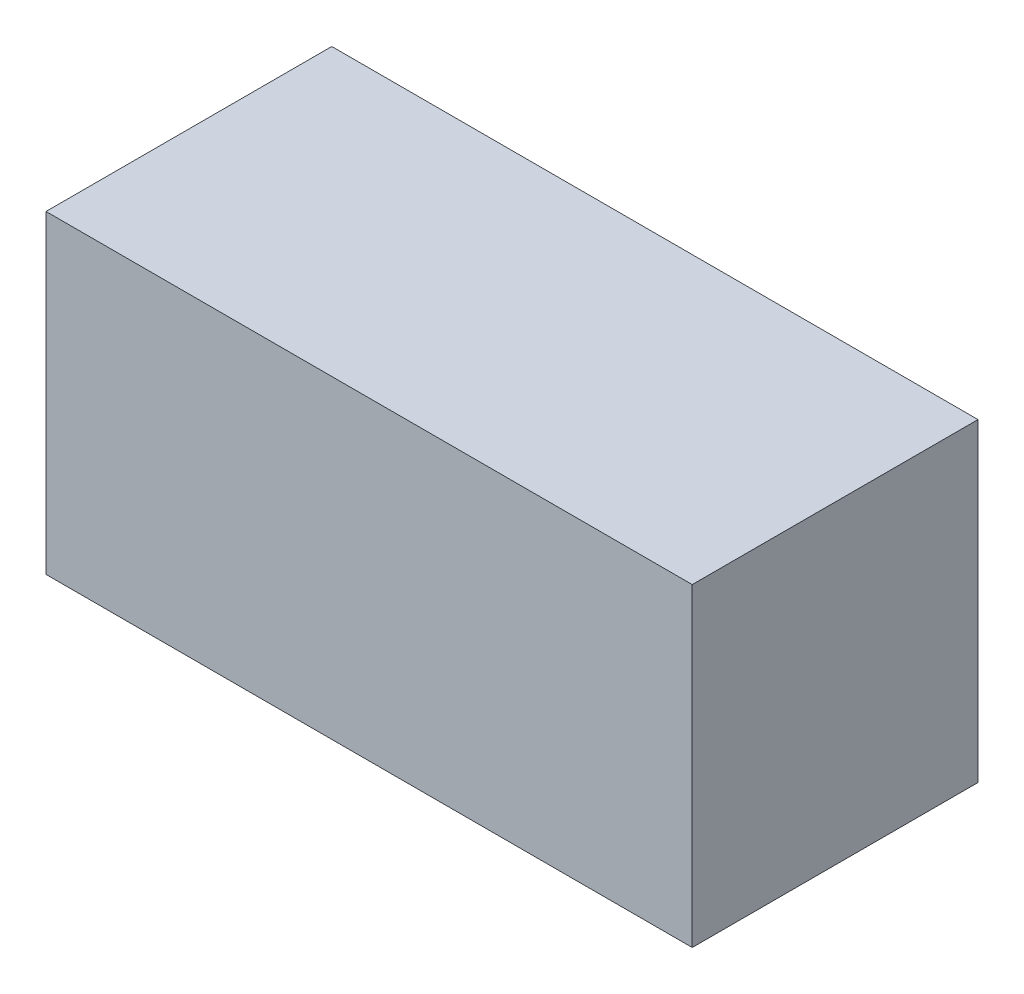
SolidWorks part; units mm, degrees
ref_plane "Front Plane" through (0, 0, 0) normal (0, 0, 1) x (1, 0, 0)
ref_plane "Top Plane" through (0, 0, 0) normal (0, 1, 0) x (1, 0, 0)
ref_plane "Right Plane" through (0, 0, 0) normal (1, 0, 0) x (0, 0, -1)
sketch "Sketch1" plane through (0, 0, 0) normal (0, 1, 0) x (1, 0, 0)
  line L1 (-280.416, -124.0028) -> (280.416, -124.0028)
  line L2 (-280.416, -124.0028) -> (-280.416, 124.0028)
  line L3 (-280.416, 124.0028) -> (280.416, 124.0028)
  line L4 (280.416, -124.0028) -> (280.416, 124.0028)
  line L5 (-280.416, -124.0028) -> (280.416, 124.0028) construction
  line L6 (-280.416, 124.0028) -> (280.416, -124.0028) construction
  point P0 (0, 0)
  dimension "D1" = 560.832
  dimension "D2" = 248.0056
extrude "Extrude1" add sketch "Sketch1" along normal mid plane 272.796
